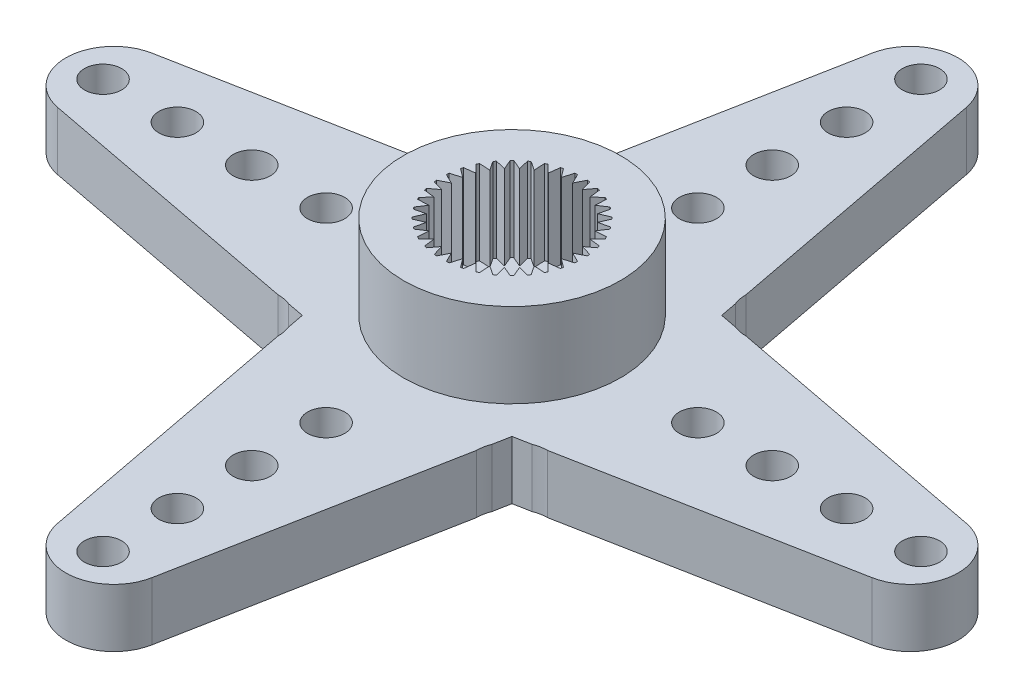
SolidWorks part; units mm, degrees
ref_plane "Front Plane" through (0, 0, 0) normal (0, 0, 1) x (1, 0, 0)
ref_plane "Top Plane" through (0, 0, 0) normal (0, 1, 0) x (1, 0, 0)
ref_plane "Right Plane" through (0, 0, 0) normal (1, 0, 0) x (0, 0, -1)
ref_plane "Plane1" through (0, 2.35, 0) normal (0, 1, 0) x (1, 0, 0)
sketch "Sketch1" plane through (0, 2.35, 0) normal (0, 1, 0) x (1, 0, 0)
  line L0 (-16.4286, -1.9) -> (-4.2305, -4.2305)
  line L1 (-4.2305, -4.2305) -> (-1.9, -16.4286)
  line L2 (1.9, -16.4286) -> (4.2305, -4.2305)
  line L3 (4.2305, -4.2305) -> (16.4286, -1.9)
  line L4 (16.4286, 1.9) -> (4.2305, 4.2305)
  line L5 (4.2305, 4.2305) -> (1.9, 16.4286)
  line L6 (-1.9, 16.4286) -> (-4.2305, 4.2305)
  line L7 (-4.2305, 4.2305) -> (-16.4286, 1.9)
  arc A0 (-1.9, -16.4286) -> (1.9, -16.4286) centre (0, -16.0656) ccw
  arc A1 (16.4286, -1.9) -> (16.4286, 1.9) centre (16.0656, 0) ccw
  arc A2 (1.9, 16.4286) -> (-1.9, 16.4286) centre (0, 16.0656) ccw
  arc A3 (-16.4286, 1.9) -> (-16.4286, -1.9) centre (-16.0656, 0) ccw
extrude "Boss-Extrude1" add sketch "Sketch1" against normal blind 2.35
sketch "Sketch2" plane through (0, 0, 0) normal (0, -1, 0) x (1, 0, 0)
  line L0 (4.1012, 4.9073) -> (4, 5.4371)
  arc A0 (4, 5.4371) -> (4.1012, 4.9073) centre (5.4371, 5.4371) ccw
extrude "Cut-Extrude1" cut sketch "Sketch2" against normal blind 2.35
sketch "Sketch3" plane through (0, 0, 0) normal (0, -1, 0) x (1, 0, 0)
  line L0 (5.4371, 4) -> (4.9073, 4.1012)
  arc A0 (4.9073, 4.1012) -> (5.4371, 4) centre (5.4371, 5.4371) ccw
extrude "Cut-Extrude2" cut sketch "Sketch3" against normal blind 2.35
sketch "Sketch4" plane through (0, 0, 0) normal (0, -1, 0) x (1, 0, 0)
  line L0 (4.9073, -4.1012) -> (5.4371, -4)
  arc A0 (5.4371, -4) -> (4.9073, -4.1012) centre (5.4371, -5.4371) ccw
extrude "Cut-Extrude3" cut sketch "Sketch4" against normal blind 2.35
sketch "Sketch5" plane through (0, 0, 0) normal (0, -1, 0) x (1, 0, 0)
  line L0 (4, -5.4371) -> (4.1012, -4.9073)
  arc A0 (4.1012, -4.9073) -> (4, -5.4371) centre (5.4371, -5.4371) ccw
extrude "Cut-Extrude4" cut sketch "Sketch5" against normal blind 2.35
sketch "Sketch6" plane through (0, 0, 0) normal (0, -1, 0) x (1, 0, 0)
  line L0 (-4.1012, -4.9073) -> (-4, -5.4371)
  arc A0 (-4, -5.4371) -> (-4.1012, -4.9073) centre (-5.4371, -5.4371) ccw
extrude "Cut-Extrude5" cut sketch "Sketch6" against normal blind 2.35
sketch "Sketch7" plane through (0, 0, 0) normal (0, -1, 0) x (1, 0, 0)
  line L0 (-5.4371, -4) -> (-4.9073, -4.1012)
  arc A0 (-4.9073, -4.1012) -> (-5.4371, -4) centre (-5.4371, -5.4371) ccw
extrude "Cut-Extrude6" cut sketch "Sketch7" against normal blind 2.35
sketch "Sketch8" plane through (0, 0, 0) normal (0, -1, 0) x (1, 0, 0)
  line L0 (-4.9073, 4.1012) -> (-5.4371, 4)
  arc A0 (-5.4371, 4) -> (-4.9073, 4.1012) centre (-5.4371, 5.4371) ccw
extrude "Cut-Extrude7" cut sketch "Sketch8" against normal blind 2.35
sketch "Sketch9" plane through (0, 0, 0) normal (0, -1, 0) x (1, 0, 0)
  line L0 (-4, 5.4371) -> (-4.1012, 4.9073)
  arc A0 (-4.1012, 4.9073) -> (-4, 5.4371) centre (-5.4371, 5.4371) ccw
extrude "Cut-Extrude8" cut sketch "Sketch9" against normal blind 2.35
sketch "Sketch10" plane through (0, 2.35, 0) normal (0, 1, 0) x (-1, 0, 0)
  circle A0 centre (0, 0) radius 4.375
extrude "Boss-Extrude2" add sketch "Sketch10" along normal blind 3.4
sketch "Sketch11" plane through (0, 5.75, 0) normal (0, 1, 0) x (-1, 0, 0)
  line L0 (0.6873, 2.7659) -> (0.4254, 2.4128)
  line L1 (0.4254, 2.4128) -> (0.3001, 2.8342)
  line L2 (0.1966, 2.8432) -> (0, 2.45)
  line L3 (0, 2.45) -> (-0.1966, 2.8432)
  line L4 (-0.3001, 2.8342) -> (-0.4254, 2.4128)
  line L5 (-0.4254, 2.4128) -> (-0.6873, 2.7659)
  line L6 (-0.7877, 2.739) -> (-0.8379, 2.3022)
  line L7 (-0.8379, 2.3022) -> (-1.1572, 2.6045)
  line L8 (-1.2513, 2.5606) -> (-1.225, 2.1218)
  line L9 (-1.225, 2.1218) -> (-1.5919, 2.364)
  line L10 (-1.677, 2.3044) -> (-1.5748, 1.8768)
  line L11 (-1.5748, 1.8768) -> (-1.9782, 2.0517)
  line L12 (-2.0517, 1.9782) -> (-1.8768, 1.5748)
  line L13 (-1.8768, 1.5748) -> (-2.3044, 1.677)
  line L14 (-2.364, 1.5919) -> (-2.1218, 1.225)
  line L15 (-2.1218, 1.225) -> (-2.5606, 1.2513)
  line L16 (-2.6045, 1.1572) -> (-2.3022, 0.8379)
  line L17 (-2.3022, 0.8379) -> (-2.739, 0.7877)
  line L18 (-2.7659, 0.6873) -> (-2.4128, 0.4254)
  line L19 (-2.4128, 0.4254) -> (-2.8342, 0.3001)
  line L20 (-2.8432, 0.1966) -> (-2.45, 0)
  line L21 (-2.45, 0) -> (-2.8432, -0.1966)
  line L22 (-2.8342, -0.3001) -> (-2.4128, -0.4254)
  line L23 (-2.4128, -0.4254) -> (-2.7659, -0.6873)
  line L24 (-2.739, -0.7877) -> (-2.3022, -0.8379)
  line L25 (-2.3022, -0.8379) -> (-2.6045, -1.1572)
  line L26 (-2.5606, -1.2513) -> (-2.1218, -1.225)
  line L27 (-2.1218, -1.225) -> (-2.364, -1.5919)
  line L28 (-2.3044, -1.677) -> (-1.8768, -1.5748)
  line L29 (-1.8768, -1.5748) -> (-2.0517, -1.9782)
  line L30 (-1.9782, -2.0517) -> (-1.5748, -1.8768)
  line L31 (-1.5748, -1.8768) -> (-1.677, -2.3044)
  line L32 (-1.5919, -2.364) -> (-1.225, -2.1218)
  line L33 (-1.225, -2.1218) -> (-1.2513, -2.5606)
  line L34 (-1.1572, -2.6045) -> (-0.8379, -2.3022)
  line L35 (-0.8379, -2.3022) -> (-0.7877, -2.739)
  line L36 (-0.6873, -2.7659) -> (-0.4254, -2.4128)
  line L37 (-0.4254, -2.4128) -> (-0.3001, -2.8342)
  line L38 (-0.1966, -2.8432) -> (0, -2.45)
  line L39 (0, -2.45) -> (0.1966, -2.8432)
  line L40 (0.3001, -2.8342) -> (0.4254, -2.4128)
  line L41 (0.4254, -2.4128) -> (0.6873, -2.7659)
  line L42 (0.7877, -2.739) -> (0.8379, -2.3022)
  line L43 (0.8379, -2.3022) -> (1.1572, -2.6045)
  line L44 (1.2513, -2.5606) -> (1.225, -2.1218)
  line L45 (1.225, -2.1218) -> (1.5919, -2.364)
  line L46 (1.677, -2.3044) -> (1.5748, -1.8768)
  line L47 (1.5748, -1.8768) -> (1.9782, -2.0517)
  line L48 (2.0517, -1.9782) -> (1.8768, -1.5748)
  line L49 (1.8768, -1.5748) -> (2.3044, -1.677)
  line L50 (2.364, -1.5919) -> (2.1218, -1.225)
  line L51 (2.1218, -1.225) -> (2.5606, -1.2513)
  line L52 (2.6045, -1.1572) -> (2.3022, -0.8379)
  line L53 (2.3022, -0.8379) -> (2.739, -0.7877)
  line L54 (2.7659, -0.6873) -> (2.4128, -0.4254)
  line L55 (2.4128, -0.4254) -> (2.8342, -0.3001)
  line L56 (2.8432, -0.1966) -> (2.45, 0)
  line L57 (2.45, 0) -> (2.8432, 0.1966)
  line L58 (2.8342, 0.3001) -> (2.4128, 0.4254)
  line L59 (2.4128, 0.4254) -> (2.7659, 0.6873)
  line L60 (2.739, 0.7877) -> (2.3022, 0.8379)
  line L61 (2.3022, 0.8379) -> (2.6045, 1.1572)
  line L62 (2.5606, 1.2513) -> (2.1218, 1.225)
  line L63 (2.1218, 1.225) -> (2.364, 1.5919)
  line L64 (2.3044, 1.677) -> (1.8768, 1.5748)
  line L65 (1.8768, 1.5748) -> (2.0517, 1.9782)
  line L66 (1.9782, 2.0517) -> (1.5748, 1.8768)
  line L67 (1.5748, 1.8768) -> (1.677, 2.3044)
  line L68 (1.5919, 2.364) -> (1.225, 2.1218)
  line L69 (1.225, 2.1218) -> (1.2513, 2.5606)
  line L70 (1.1572, 2.6045) -> (0.8379, 2.3022)
  line L71 (0.8379, 2.3022) -> (0.7877, 2.739)
  arc A0 (0.3001, 2.8342) -> (0.1966, 2.8432) centre (0, 0) ccw
  arc A1 (-0.1966, 2.8432) -> (-0.3001, 2.8342) centre (0, 0) ccw
  arc A2 (-0.6873, 2.7659) -> (-0.7877, 2.739) centre (0, 0) ccw
  arc A3 (-1.1572, 2.6045) -> (-1.2513, 2.5606) centre (0, 0) ccw
  arc A4 (-1.5919, 2.364) -> (-1.677, 2.3044) centre (0, 0) ccw
  arc A5 (-1.9782, 2.0517) -> (-2.0517, 1.9782) centre (0, 0) ccw
  arc A6 (-2.3044, 1.677) -> (-2.364, 1.5919) centre (0, 0) ccw
  arc A7 (-2.5606, 1.2513) -> (-2.6045, 1.1572) centre (0, 0) ccw
  arc A8 (-2.739, 0.7877) -> (-2.7659, 0.6873) centre (0, 0) ccw
  arc A9 (-2.8342, 0.3001) -> (-2.8432, 0.1966) centre (0, 0) ccw
  arc A10 (-2.8432, -0.1966) -> (-2.8342, -0.3001) centre (0, 0) ccw
  arc A11 (-2.7659, -0.6873) -> (-2.739, -0.7877) centre (0, 0) ccw
  arc A12 (-2.6045, -1.1572) -> (-2.5606, -1.2513) centre (0, 0) ccw
  arc A13 (-2.364, -1.5919) -> (-2.3044, -1.677) centre (0, 0) ccw
  arc A14 (-2.0517, -1.9782) -> (-1.9782, -2.0517) centre (0, 0) ccw
  arc A15 (-1.677, -2.3044) -> (-1.5919, -2.364) centre (0, 0) ccw
  arc A16 (-1.2513, -2.5606) -> (-1.1572, -2.6045) centre (0, 0) ccw
  arc A17 (-0.7877, -2.739) -> (-0.6873, -2.7659) centre (0, 0) ccw
  arc A18 (-0.3001, -2.8342) -> (-0.1966, -2.8432) centre (0, 0) ccw
  arc A19 (0.1966, -2.8432) -> (0.3001, -2.8342) centre (0, 0) ccw
  arc A20 (0.6873, -2.7659) -> (0.7877, -2.739) centre (0, 0) ccw
  arc A21 (1.1572, -2.6045) -> (1.2513, -2.5606) centre (0, 0) ccw
  arc A22 (1.5919, -2.364) -> (1.677, -2.3044) centre (0, 0) ccw
  arc A23 (1.9782, -2.0517) -> (2.0517, -1.9782) centre (0, 0) ccw
  arc A24 (2.3044, -1.677) -> (2.364, -1.5919) centre (0, 0) ccw
  arc A25 (2.5606, -1.2513) -> (2.6045, -1.1572) centre (0, 0) ccw
  arc A26 (2.739, -0.7877) -> (2.7659, -0.6873) centre (0, 0) ccw
  arc A27 (2.8342, -0.3001) -> (2.8432, -0.1966) centre (0, 0) ccw
  arc A28 (2.8432, 0.1966) -> (2.8342, 0.3001) centre (0, 0) ccw
  arc A29 (2.7659, 0.6873) -> (2.739, 0.7877) centre (0, 0) ccw
  arc A30 (2.6045, 1.1572) -> (2.5606, 1.2513) centre (0, 0) ccw
  arc A31 (2.364, 1.5919) -> (2.3044, 1.677) centre (0, 0) ccw
  arc A32 (2.0517, 1.9782) -> (1.9782, 2.0517) centre (0, 0) ccw
  arc A33 (1.677, 2.3044) -> (1.5919, 2.364) centre (0, 0) ccw
  arc A34 (1.2513, 2.5606) -> (1.1572, 2.6045) centre (0, 0) ccw
  arc A35 (0.7877, 2.739) -> (0.6873, 2.7659) centre (0, 0) ccw
extrude "Cut-Extrude9" cut sketch "Sketch11" against normal blind 3.4
hole_wizard "Hole1" positions "Sketch13" profile "Sketch12" legacy
sketch "Sketch13" plane through (0, 0, 0) normal (0, -1, 0) x (-1, 0, 0)
  point P0 (0, 0)
sketch "Sketch12" plane through (0, 0, 0) normal (1, 0, 0) x (0, 0, -1)
  line L0 (0, 0) -> (0, 0.3)
  line L1 (0, 0.3) -> (4.4, 0.3)
  line L2 (4.4, 0.3) -> (4.4, 0)
  line L3 (4.4, 0) -> (0, 0)
  line L4 (0, 110) -> (0, -10) construction
  dimension "Diameter" = 8.8
  dimension "Depth" = 0.3
sketch "Sketch14" plane through (0, 0, 0) normal (0, 0, 1) x (1, 0, 0)
  line L0 (3.25, 0.3) -> (0, 0.3)
  line L1 (0, 0.3) -> (0, 0)
  line L2 (0, 0) -> (3.25, 0)
  line L3 (3.25, 0) -> (3.25, 0.3)
  line L4 (0, 0.3) -> (0, 0) construction
revolve "Revolve1" add sketch "Sketch14" angle 360 about L4
hole_wizard "#00 Clearance Hole1" positions "Sketch16" profile "Sketch15" hole size "#00" standard "ANSI Inch"
sketch "Sketch16" plane through (0, 2.35, 0) normal (0, 1, 0) x (1, 0, 0)
  point P0 (0, -7.5)
  point P1 (0, -10.5)
  point P2 (0, -13.5)
  point P3 (0, -16.5)
  point P4 (7.5, 0)
  point P5 (10.5, 0)
  point P6 (13.5, 0)
  point P7 (16.5, 0)
  point P8 (0, 7.5)
  point P9 (0, 10.5)
  point P10 (0, 13.5)
  point P11 (0, 16.5)
  point P12 (-7.5, 0)
  point P13 (-10.5, 0)
  point P14 (-13.5, 0)
  point P15 (-16.5, 0)
sketch "Sketch15" plane through (0, 2.35, 7.5) normal (1, 0, 0) x (0, 0, 1)
  line L0 (0, 0) -> (0, 2.35)
  line L1 (0, 2.35) -> (0.75, 2.35)
  line L2 (0.75, 2.35) -> (0.75, 0)
  line L5 (0.75, 0) -> (0, 0)
  line L11 (0, -6.35) -> (0, 107.95) construction
  dimension "Thru Hole Dia." = 1.5
  dimension "Thru Hole Depth" = 2.35
hole_wizard "CBORE for #3 Binding Head Machine Screw1" positions "Sketch18" profile "Sketch17" counterbore size "#3" standard "ANSI Inch"
sketch "Sketch18" plane through (0, 0, 0) normal (0, -1, 0) x (-1, 0, 0)
  point P0 (0, 0)
sketch "Sketch17" plane through (0, 0, 0) normal (1, 0, 0) x (0, 0, -1)
  line L0 (0, 0) -> (0, 5.75)
  line L1 (0, 5.75) -> (1.5, 5.75)
  line L3 (1.5, 5.75) -> (1.5, 0.3)
  line L4 (1.5, 0.3) -> (2.75, 0.3)
  line L5 (2.75, 0.3) -> (2.75, 0)
  line L7 (2.75, 0) -> (0, 0)
  line L11 (0, -6.35) -> (0, 107.95) construction
  dimension "Thru Hole Dia." = 3
  dimension "Thru Hole Depth" = 5.75
  dimension "C'Bore Dia." = 5.5
  dimension "C'Bore Depth" = 0.3
